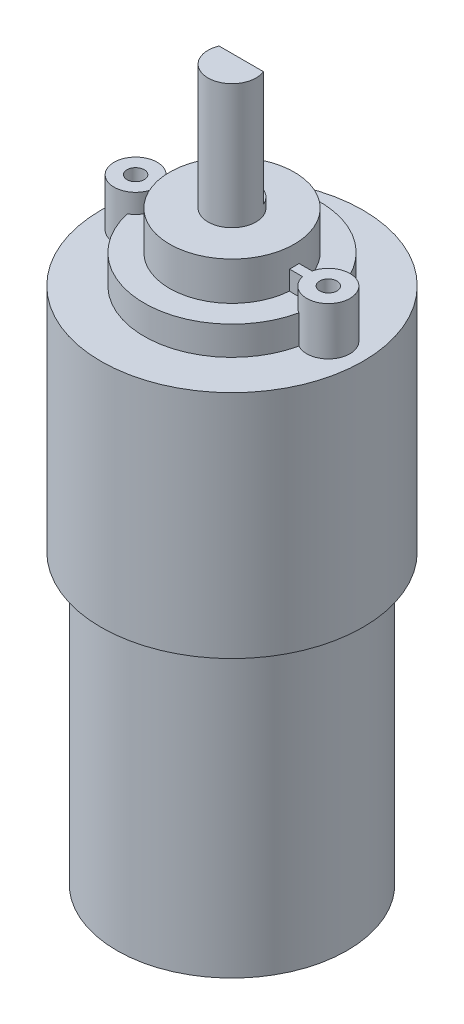
SolidWorks part; units mm, degrees
ref_plane "Alzado" through (0, 0, 0) normal (0, 0, 1) x (1, 0, 0)
ref_plane "Planta" through (0, 0, 0) normal (0, 1, 0) x (1, 0, 0)
ref_plane "Vista lateral" through (0, 0, 0) normal (1, 0, 0) x (0, 0, -1)
sketch "Croquis1" plane through (0, 0, 0) normal (0, 0, 1) x (1, 0, 0)
  line L0 (0, 65.6872) -> (0, -89.1873) construction
  line L1 (0, 30.5) -> (-6.5, 30.5)
  line L2 (-6.5, 30.5) -> (-6.5, 26.5)
  line L3 (-6.5, 26.5) -> (-9.15, 26.5)
  line L4 (-9.15, 26.5) -> (-9.15, 23.5)
  line L5 (-9.15, 23.5) -> (-13.65, 23.5)
  line L6 (-13.65, 23.5) -> (-13.65, -0.5)
  line L7 (-13.65, -0.5) -> (-12, -0.5)
  line L8 (-12, -0.5) -> (-12, -30.5)
  line L9 (-12, -30.5) -> (0, -30.5)
  line L10 (0, -30.5) -> (0, 30.5)
  line L11 (0, 30.5) -> (0, 43.5)
  line L12 (0, 43.5) -> (-2.5, 43.5)
  line L13 (-2.5, 43.5) -> (-2.5, 30.5)
  line L14 (-2.5, 30.5) -> (0, 30.5)
  point P5 (0, 0)
  dimension "D1" = 6.5
  dimension "D2" = 4
  dimension "D3" = 9.15
  dimension "D4" = 13.65
  dimension "D5" = 24
  dimension "D6" = 30
  dimension "D7" = 3
  dimension "D8" = 12
  dimension "D9" = 13
  dimension "D10" = 2.5
revolve "Revolución1" add sketch "Croquis1" angle 360 about L0
sketch "Croquis2" plane through (0, 43.5, 0) normal (0, 1, 0) x (1, 0, 0)
  line L0 (-2.3083, 0.96) -> (2.3083, 0.96)
  circle A1 centre (0, 0) radius 2.5
  circle A2 centre (0, 0) radius 2.5
  circle M3 centre (0, 0) radius 2.5
  dimension "D2" = 0.96
  dimension "D1" = 0
extrude "Cortar-Extruir1" cut sketch "Croquis2" against normal blind 12 contours L0 M3
sketch "Croquis4" plane through (0, 23.5, 0) normal (0, 1, 0) x (1, 0, 0)
  line L0 (0, 5.4331) -> (0, -4.2682) construction
  line L1 (9, 0.5) -> (-9, 0.5)
  line L2 (0, 0.5) -> (0, -0.5)
  line L3 (9, -0.5) -> (-9, -0.5)
  line L4 (-9, 0.5) -> (-9, -0.5)
  line L5 (-12.29, 7.8034) -> (-12.29, -7.8344) construction
  line L6 (0, 0) -> (-16.243, 0) construction
  line L7 (9, 0.5) -> (9, -0.5)
  circle A0 centre (-10.04, 0) radius 2.25
  circle A1 centre (-10.04, 0) radius 0.9
  circle A2 centre (10.04, 0) radius 0.9
  circle A3 centre (10.04, 0) radius 2.25
  point P10 (0, 0)
  circle M11 centre (0, 0) radius 9.15
  dimension "D1" = 1.8
  dimension "D2" = 4.5
  dimension "D3" = 1
  dimension "D4" = 12.29
  dimension "D5" = 9
extrude "Saliente-Extruir1" add sketch "Croquis4" along normal blind 5 contours A1 A0 M11 | A1 A0 L3 L4 L1 M11 | A0 L3 L2 L1 | L3 A3 L1 L2 | A3 A2 L1 L7 L3 M11 | A3 L3 L7 L1 | A3 A2 M11 | L3 A0 L1 L4
